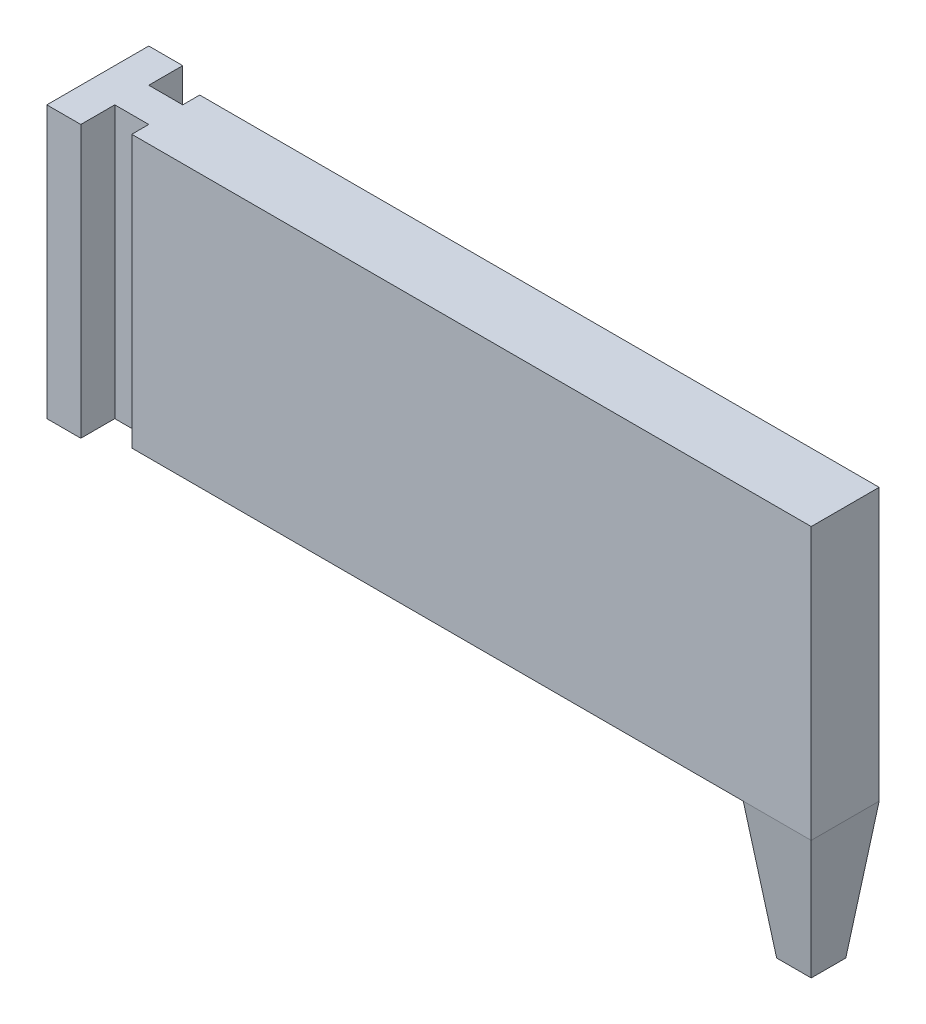
SolidWorks part; units mm, degrees
ref_plane "Front Plane" through (0, 0, 0) normal (0, 0, 1) x (1, 0, 0)
ref_plane "Top Plane" through (0, 0, 0) normal (0, 1, 0) x (1, 0, 0)
ref_plane "Right Plane" through (0, 0, 0) normal (1, 0, 0) x (0, 0, -1)
sketch "Sketch2" plane through (0, 0, 0) normal (0, 1, 0) x (1, 0, 0)
  line L0 (-10, 7.5) -> (-10, -7.5)
  line L1 (-10, -7.5) -> (-5, -7.5)
  line L2 (-5, -7.5) -> (-5, -2.5)
  line L3 (-5, -2.5) -> (0, -2.5)
  line L4 (0, -2.5) -> (0, 2.5)
  line L5 (0, 2.5) -> (-5, 2.5)
  line L6 (-5, 2.5) -> (-5, 7.5)
  line L7 (-5, 7.5) -> (-10, 7.5)
  point P2 (0, 0)
  dimension "D1" = 5
extrude "Boss-Extrude1" add sketch "Sketch2" along normal blind 40
sketch "Sketch3" plane through (0, 0, 0) normal (0, 0, 1) x (1, 0, 0)
  line L0 (0, 0) -> (100, 0)
  line L3 (100, 0) -> (100, 40)
  line L4 (100, 40) -> (0, 40)
  line L6 (0, 40) -> (0, 0)
  point P4 (90.5311, 0)
  point P10 (100, 0)
  point P11 (0, 0)
  point P12 (100, 0)
  point P13 (100, 0.7617)
  dimension "D4" = 100
extrude "Boss-Extrude2" add sketch "Sketch3" along normal blind 5 and the other way blind 5
sketch "Sketch4" plane through (0, 0, 0) normal (0, -1, 0) x (1, 0, 0)
  line L0 (0, 5) -> (100, 5) construction
  line L1 (100, -5) -> (90, -5)
  line L2 (100, -5) -> (100, 5)
  line L3 (100, 5) -> (90, 5)
  line L4 (90, -5) -> (90, 5)
extrude "Boss-Extrude3" add sketch "Sketch4" along normal blind 20 draft 7
